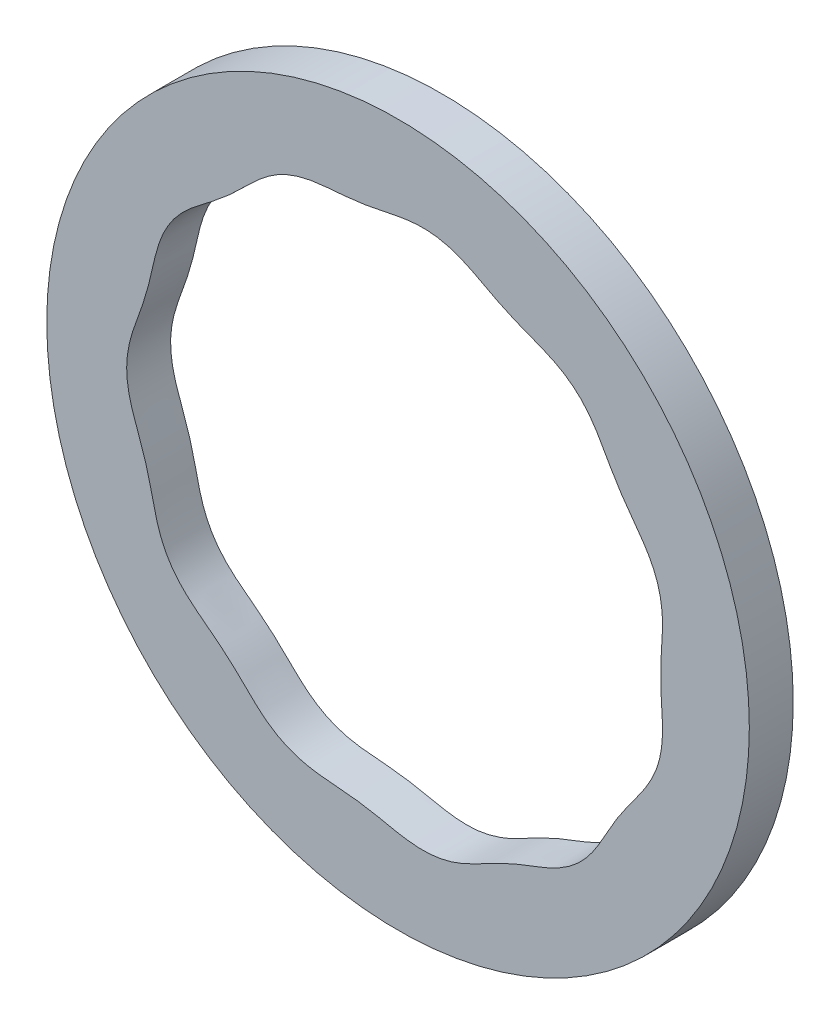
SolidWorks part; units mm, degrees
ref_plane "Front Plane" through (0, 0, 0) normal (0, 0, 1) x (1, 0, 0)
ref_plane "Top Plane" through (0, 0, 0) normal (0, 1, 0) x (1, 0, 0)
ref_plane "Right Plane" through (0, 0, 0) normal (1, 0, 0) x (0, 0, -1)
curve "Curve1"
sketch "Sketch2" plane through (0, 0, 0) normal (0, 0, 1) x (1, 0, 0)
  circle A0 centre (0, 0) radius 40
  dimension "D1" = 80
extrude "Boss-Extrude1" add sketch "Sketch2" along normal blind 5
sketch "Sketch3" plane through (0, 0, 0) normal (0, 0, 1) x (1, 0, 0)
  spline S3 degree 3 poles (-28.7034, -8.3743) (-28.552, -8.8888) (-28.4221, -9.3767) (-28.1806, -10.3578) (-28.0695, -10.8512) (-27.7343, -12.3306) (-27.5067, -13.3158) (-27.0032, -14.7464) (-26.8088, -15.216) (-26.3514, -16.1336) (-26.0943, -16.5702) (-25.524, -17.3996) (-25.2108, -17.7924) (-24.5338, -18.5385) (-24.1697, -18.892) (-23.0226, -19.9074) (-22.197, -20.5141) (-20.9796, -21.4483) (-20.5771, -21.7635) (-19.7884, -22.4128) (-19.4023, -22.747) (-18.6463, -23.434) (-18.2767, -23.7872) (-17.5443, -24.5015) (-17.1816, -24.8627) (-16.4457, -25.573) (-16.0714, -25.9221) (-15.297, -26.5828) (-14.897, -26.8938) (-14.0618, -27.4626) (-13.6265, -27.7204) (-12.7155, -28.1751) (-12.2383, -28.3717) (-11.275, -28.6928) (-10.7852, -28.8195) (-9.7925, -29.0185) (-9.2896, -29.0909) (-8.2764, -29.2047) (-7.767, -29.2462) (-6.7486, -29.3279) (-6.2393, -29.3681) (-5.2235, -29.4685) (-4.7171, -29.5286) (-3.7078, -29.6751) (-3.2051, -29.7616) (-1.7009, -30.0495) (-0.7041, -30.2836) (0.8041, -30.543) (1.3092, -30.6129) (2.3275, -30.6954) (2.836, -30.7075) (3.8443, -30.662) (4.3451, -30.6049) (5.3398, -30.419) (5.837, -30.2889) (7.2863, -29.8095) (8.1988, -29.3688) (9.5468, -28.6609) (9.9933, -28.4184) (10.8906, -27.9434) (11.3418, -27.7116) (12.2541, -27.2703) (12.7153, -27.061) (13.6475, -26.6648) (14.1185, -26.4777) (15.5375, -25.9299) (16.4913, -25.5825) (17.8669, -24.9368) (18.3148, -24.7008) (19.171, -24.1782) (19.5807, -23.8911) (20.1642, -23.4174) (20.3537, -23.2524) (20.7222, -22.9078) (20.902, -22.7275) (21.4195, -22.1713) (21.7355, -21.7813) (22.6155, -20.5658) (23.1096, -19.6939) (23.8417, -18.3801) (24.0851, -17.9417) (24.5868, -17.0749) (24.8455, -16.6467) (25.3841, -15.8044) (25.664, -15.3903) (26.2401, -14.573) (26.5364, -14.1698) (27.4259, -12.9607) (28.018, -12.1541) (28.7724, -10.855) (28.9992, -10.4121) (29.3907, -9.5052) (29.5559, -9.0408) (29.8214, -8.0888) (29.9219, -7.5992) (30.0589, -6.6064) (30.0949, -6.1088) (30.131, -4.6134) (30.0588, -3.613) (29.9654, -2.1144) (29.9371, -1.6148) (29.9025, -0.6148) (29.8962, -0.1144) (29.9087, 0.8872) (29.9276, 1.3884) (29.9809, 2.3914) (30.0151, 2.8931) (30.1058, 4.3979) (30.1462, 5.4004) (30.0268, 6.8982) (29.9578, 7.3964) (29.7479, 8.3905) (29.6044, 8.8913) (29.0809, 10.3245) (28.6037, 11.2028) (27.5089, 12.8747) (26.8965, 13.6714) (26.0148, 14.8888) (25.7267, 15.2981) (25.1717, 16.1294) (24.9048, 16.5515) (24.3906, 17.4074) (24.1432, 17.8413) (23.6551, 18.7134) (23.4143, 19.1515) (22.6685, 20.4509) (22.1364, 21.2948) (21.332, 22.2599) (21.1636, 22.4494) (20.8165, 22.8142) (20.6377, 22.9896) (20.0862, 23.4945) (19.6978, 23.8027) (18.8821, 24.3659) (18.4546, 24.6207) (17.5673, 25.0859) (17.1075, 25.2959) (16.1782, 25.6862) (15.7073, 25.8675) (14.7645, 26.2284) (14.2929, 26.4082) (13.3575, 26.7851) (12.8938, 26.9824) (11.9771, 27.4004) (11.5242, 27.6211) (10.6265, 28.0807) (10.1816, 28.319) (9.2915, 28.7954) (8.8461, 29.0327) (7.9432, 29.4808) (7.4861, 29.6905) (6.5565, 30.0579) (6.0835, 30.216) (5.1174, 30.4684) (4.6224, 30.5628) (3.618, 30.6806) (3.1174, 30.7032) (2.1191, 30.6854) (1.6213, 30.6448) (0.6279, 30.5174) (0.1319, 30.4306) (-0.8571, 30.2373) (-1.3503, 30.1316) (-2.3377, 29.9276) (-2.832, 29.8298) (-3.824, 29.6568) (-4.3216, 29.582) (-5.3206, 29.4573) (-5.8218, 29.407) (-7.3284, 29.2767) (-8.3368, 29.217) (-9.8324, 29.0102) (-10.3301, 28.9206) (-11.3048, 28.6831) (-11.7811, 28.536) (-12.7089, 28.1773) (-13.1604, 27.9659) (-13.8187, 27.5999) (-14.0356, 27.4693) (-14.4577, 27.1962) (-14.6635, 27.0534) (-15.669, 26.3117) (-16.3964, 25.6276) (-17.4685, 24.5792) (-17.8233, 24.2266) (-18.5428, 23.5332) (-18.9074, 23.1922) (-19.6526, 22.5291) (-20.0334, 22.2072) (-20.8091, 21.5801) (-21.204, 21.2749) (-22.3947, 20.3661) (-23.1955, 19.7685) (-24.3044, 18.7634) (-24.6596, 18.4087) (-25.3153, 17.6645) (-25.6173, 17.2739) (-26.1656, 16.453) (-26.4117, 16.0226) (-26.849, 15.1225) (-27.036, 14.6609) (-27.5211, 13.2572) (-27.7432, 12.292) (-28.0714, 10.8427) (-28.1805, 10.3595) (-28.4165, 9.3983) (-28.5435, 8.9203) (-28.8213, 7.9713) (-28.9723, 7.5003) (-29.2924, 6.5636) (-29.4615, 6.0979) (-29.9694, 4.7009) (-30.3061, 3.7691) (-30.6611, 2.3275) (-30.755, 1.8399) (-30.8472, 1.0943) (-30.8696, 0.8448) (-30.8971, 0.3519) (-30.9022, 0.1074) (-30.8869, -1.1059) (-30.7403, -2.0467) (-30.265, -3.8876) (-29.9377, -4.788) (-29.4467, -6.1387) (-29.2835, -6.589) (-29.0519, -7.2675) (-28.9767, -7.4941) (-28.868, -7.8349) (-28.8323, -7.9486) (-28.7799, -8.1194) (-28.7626, -8.1764) (-28.7368, -8.2619) (-28.7283, -8.2905) (-28.7113, -8.3475) (-28.7034, -8.3743) (-28.552, -8.8888) (-28.4221, -9.3767) knots -0.000488 -0.000488 0 0 0.007812 0.007812 0.015625 0.015625 0.03125 0.03125 0.039062 0.039062 0.046875 0.046875 0.054687 0.054687 0.0625 0.0625 0.078125 0.078125 0.085937 0.085937 0.09375 0.09375 0.101562 0.101562 0.109375 0.109375 0.117187 0.117187 0.125 0.125 0.132812 0.132812 0.140625 0.140625 0.148437 0.148437 0.15625 0.15625 0.164062 0.164062 0.171875 0.171875 0.179687 0.179687 0.1875 0.1875 0.203125 0.203125 0.210937 0.210937 0.21875 0.21875 0.226562 0.226562 0.234375 0.234375 0.25 0.25 0.257812 0.257812 0.265625 0.265625 0.273437 0.273437 0.28125 0.28125 0.296875 0.296875 0.304687 0.304687 0.3125 0.3125 0.316406 0.316406 0.320312 0.320312 0.328125 0.328125 0.34375 0.34375 0.351562 0.351562 0.359375 0.359375 0.367187 0.367187 0.375 0.375 0.390625 0.390625 0.398437 0.398437 0.40625 0.40625 0.414062 0.414062 0.421875 0.421875 0.4375 0.4375 0.445312 0.445312 0.453125 0.453125 0.460937 0.460937 0.46875 0.46875 0.484375 0.484375 0.492187 0.492187 0.5 0.5 0.515625 0.515625 0.53125 0.53125 0.539062 0.539062 0.546875 0.546875 0.554687 0.554687 0.5625 0.5625 0.578125 0.578125 0.582031 0.582031 0.585937 0.585937 0.59375 0.59375 0.601562 0.601562 0.609375 0.609375 0.617187 0.617187 0.625 0.625 0.632812 0.632812 0.640625 0.640625 0.648437 0.648437 0.65625 0.65625 0.664062 0.664062 0.671875 0.671875 0.679687 0.679687 0.6875 0.6875 0.695312 0.695312 0.703125 0.703125 0.710937 0.710937 0.71875 0.71875 0.726562 0.726562 0.734375 0.734375 0.75 0.75 0.757812 0.757812 0.765625 0.765625 0.773437 0.773437 0.777344 0.777344 0.78125 0.78125 0.796875 0.796875 0.804687 0.804687 0.8125 0.8125 0.820312 0.820312 0.828125 0.828125 0.84375 0.84375 0.851562 0.851562 0.859375 0.859375 0.867187 0.867187 0.875 0.875 0.890625 0.890625 0.898437 0.898437 0.90625 0.90625 0.914062 0.914062 0.921875 0.921875 0.9375 0.9375 0.945312 0.945312 0.949219 0.949219 0.953125 0.953125 0.96875 0.96875 0.984375 0.984375 0.992187 0.992187 0.996094 0.996094 0.998047 0.998047 0.999023 0.999023 0.999512 0.999512 1 1 1.007812 1.007812 1.015625 only from (-28.6945, -8.4046) to (-28.6945, -8.4046)
  spline S4 degree 3 poles (-28.7034, -8.3743) (-28.552, -8.8888) (-28.4221, -9.3767) (-28.1806, -10.3578) (-28.0695, -10.8512) (-27.7343, -12.3306) (-27.5067, -13.3158) (-27.0032, -14.7464) (-26.8088, -15.216) (-26.3514, -16.1336) (-26.0943, -16.5702) (-25.524, -17.3996) (-25.2108, -17.7924) (-24.5338, -18.5385) (-24.1697, -18.892) (-23.0226, -19.9074) (-22.197, -20.5141) (-20.9796, -21.4483) (-20.5771, -21.7635) (-19.7884, -22.4128) (-19.4023, -22.747) (-18.6463, -23.434) (-18.2767, -23.7872) (-17.5443, -24.5015) (-17.1816, -24.8627) (-16.4457, -25.573) (-16.0714, -25.9221) (-15.297, -26.5828) (-14.897, -26.8938) (-14.0618, -27.4626) (-13.6265, -27.7204) (-12.7155, -28.1751) (-12.2383, -28.3717) (-11.275, -28.6928) (-10.7852, -28.8195) (-9.7925, -29.0185) (-9.2896, -29.0909) (-8.2764, -29.2047) (-7.767, -29.2462) (-6.7486, -29.3279) (-6.2393, -29.3681) (-5.2235, -29.4685) (-4.7171, -29.5286) (-3.7078, -29.6751) (-3.2051, -29.7616) (-1.7009, -30.0495) (-0.7041, -30.2836) (0.8041, -30.543) (1.3092, -30.6129) (2.3275, -30.6954) (2.836, -30.7075) (3.8443, -30.662) (4.3451, -30.6049) (5.3398, -30.419) (5.837, -30.2889) (7.2863, -29.8095) (8.1988, -29.3688) (9.5468, -28.6609) (9.9933, -28.4184) (10.8906, -27.9434) (11.3418, -27.7116) (12.2541, -27.2703) (12.7153, -27.061) (13.6475, -26.6648) (14.1185, -26.4777) (15.5375, -25.9299) (16.4913, -25.5825) (17.8669, -24.9368) (18.3148, -24.7008) (19.171, -24.1782) (19.5807, -23.8911) (20.1642, -23.4174) (20.3537, -23.2524) (20.7222, -22.9078) (20.902, -22.7275) (21.4195, -22.1713) (21.7355, -21.7813) (22.6155, -20.5658) (23.1096, -19.6939) (23.8417, -18.3801) (24.0851, -17.9417) (24.5868, -17.0749) (24.8455, -16.6467) (25.3841, -15.8044) (25.664, -15.3903) (26.2401, -14.573) (26.5364, -14.1698) (27.4259, -12.9607) (28.018, -12.1541) (28.7724, -10.855) (28.9992, -10.4121) (29.3907, -9.5052) (29.5559, -9.0408) (29.8214, -8.0888) (29.9219, -7.5992) (30.0589, -6.6064) (30.0949, -6.1088) (30.131, -4.6134) (30.0588, -3.613) (29.9654, -2.1144) (29.9371, -1.6148) (29.9025, -0.6148) (29.8962, -0.1144) (29.9087, 0.8872) (29.9276, 1.3884) (29.9809, 2.3914) (30.0151, 2.8931) (30.1058, 4.3979) (30.1462, 5.4004) (30.0268, 6.8982) (29.9578, 7.3964) (29.7479, 8.3905) (29.6044, 8.8913) (29.0809, 10.3245) (28.6037, 11.2028) (27.5089, 12.8747) (26.8965, 13.6714) (26.0148, 14.8888) (25.7267, 15.2981) (25.1717, 16.1294) (24.9048, 16.5515) (24.3906, 17.4074) (24.1432, 17.8413) (23.6551, 18.7134) (23.4143, 19.1515) (22.6685, 20.4509) (22.1364, 21.2948) (21.332, 22.2599) (21.1636, 22.4494) (20.8165, 22.8142) (20.6377, 22.9896) (20.0862, 23.4945) (19.6978, 23.8027) (18.8821, 24.3659) (18.4546, 24.6207) (17.5673, 25.0859) (17.1075, 25.2959) (16.1782, 25.6862) (15.7073, 25.8675) (14.7645, 26.2284) (14.2929, 26.4082) (13.3575, 26.7851) (12.8938, 26.9824) (11.9771, 27.4004) (11.5242, 27.6211) (10.6265, 28.0807) (10.1816, 28.319) (9.2915, 28.7954) (8.8461, 29.0327) (7.9432, 29.4808) (7.4861, 29.6905) (6.5565, 30.0579) (6.0835, 30.216) (5.1174, 30.4684) (4.6224, 30.5628) (3.618, 30.6806) (3.1174, 30.7032) (2.1191, 30.6854) (1.6213, 30.6448) (0.6279, 30.5174) (0.1319, 30.4306) (-0.8571, 30.2373) (-1.3503, 30.1316) (-2.3377, 29.9276) (-2.832, 29.8298) (-3.824, 29.6568) (-4.3216, 29.582) (-5.3206, 29.4573) (-5.8218, 29.407) (-7.3284, 29.2767) (-8.3368, 29.217) (-9.8324, 29.0102) (-10.3301, 28.9206) (-11.3048, 28.6831) (-11.7811, 28.536) (-12.7089, 28.1773) (-13.1604, 27.9659) (-13.8187, 27.5999) (-14.0356, 27.4693) (-14.4577, 27.1962) (-14.6635, 27.0534) (-15.669, 26.3117) (-16.3964, 25.6276) (-17.4685, 24.5792) (-17.8233, 24.2266) (-18.5428, 23.5332) (-18.9074, 23.1922) (-19.6526, 22.5291) (-20.0334, 22.2072) (-20.8091, 21.5801) (-21.204, 21.2749) (-22.3947, 20.3661) (-23.1955, 19.7685) (-24.3044, 18.7634) (-24.6596, 18.4087) (-25.3153, 17.6645) (-25.6173, 17.2739) (-26.1656, 16.453) (-26.4117, 16.0226) (-26.849, 15.1225) (-27.036, 14.6609) (-27.5211, 13.2572) (-27.7432, 12.292) (-28.0714, 10.8427) (-28.1805, 10.3595) (-28.4165, 9.3983) (-28.5435, 8.9203) (-28.8213, 7.9713) (-28.9723, 7.5003) (-29.2924, 6.5636) (-29.4615, 6.0979) (-29.9694, 4.7009) (-30.3061, 3.7691) (-30.6611, 2.3275) (-30.755, 1.8399) (-30.8472, 1.0943) (-30.8696, 0.8448) (-30.8971, 0.3519) (-30.9022, 0.1074) (-30.8869, -1.1059) (-30.7403, -2.0467) (-30.265, -3.8876) (-29.9377, -4.788) (-29.4467, -6.1387) (-29.2835, -6.589) (-29.0519, -7.2675) (-28.9767, -7.4941) (-28.868, -7.8349) (-28.8323, -7.9486) (-28.7799, -8.1194) (-28.7626, -8.1764) (-28.7368, -8.2619) (-28.7283, -8.2905) (-28.7113, -8.3475) (-28.7034, -8.3743) (-28.552, -8.8888) (-28.4221, -9.3767) knots -0.000488 -0.000488 0 0 0.007812 0.007812 0.015625 0.015625 0.03125 0.03125 0.039062 0.039062 0.046875 0.046875 0.054687 0.054687 0.0625 0.0625 0.078125 0.078125 0.085937 0.085937 0.09375 0.09375 0.101562 0.101562 0.109375 0.109375 0.117187 0.117187 0.125 0.125 0.132812 0.132812 0.140625 0.140625 0.148437 0.148437 0.15625 0.15625 0.164062 0.164062 0.171875 0.171875 0.179687 0.179687 0.1875 0.1875 0.203125 0.203125 0.210937 0.210937 0.21875 0.21875 0.226562 0.226562 0.234375 0.234375 0.25 0.25 0.257812 0.257812 0.265625 0.265625 0.273437 0.273437 0.28125 0.28125 0.296875 0.296875 0.304687 0.304687 0.3125 0.3125 0.316406 0.316406 0.320312 0.320312 0.328125 0.328125 0.34375 0.34375 0.351562 0.351562 0.359375 0.359375 0.367187 0.367187 0.375 0.375 0.390625 0.390625 0.398437 0.398437 0.40625 0.40625 0.414062 0.414062 0.421875 0.421875 0.4375 0.4375 0.445312 0.445312 0.453125 0.453125 0.460937 0.460937 0.46875 0.46875 0.484375 0.484375 0.492187 0.492187 0.5 0.5 0.515625 0.515625 0.53125 0.53125 0.539062 0.539062 0.546875 0.546875 0.554687 0.554687 0.5625 0.5625 0.578125 0.578125 0.582031 0.582031 0.585937 0.585937 0.59375 0.59375 0.601562 0.601562 0.609375 0.609375 0.617187 0.617187 0.625 0.625 0.632812 0.632812 0.640625 0.640625 0.648437 0.648437 0.65625 0.65625 0.664062 0.664062 0.671875 0.671875 0.679687 0.679687 0.6875 0.6875 0.695312 0.695312 0.703125 0.703125 0.710937 0.710937 0.71875 0.71875 0.726562 0.726562 0.734375 0.734375 0.75 0.75 0.757812 0.757812 0.765625 0.765625 0.773437 0.773437 0.777344 0.777344 0.78125 0.78125 0.796875 0.796875 0.804687 0.804687 0.8125 0.8125 0.820312 0.820312 0.828125 0.828125 0.84375 0.84375 0.851562 0.851562 0.859375 0.859375 0.867187 0.867187 0.875 0.875 0.890625 0.890625 0.898437 0.898437 0.90625 0.90625 0.914062 0.914062 0.921875 0.921875 0.9375 0.9375 0.945312 0.945312 0.949219 0.949219 0.953125 0.953125 0.96875 0.96875 0.984375 0.984375 0.992187 0.992187 0.996094 0.996094 0.998047 0.998047 0.999023 0.999023 0.999512 0.999512 1 1 1.007812 1.007812 1.015625 only from (-28.6945, -8.4046) to (-28.6945, -8.4046)
  dimension "D1" = 0.4
extrude "Cut-Extrude1" cut sketch "Sketch3" along normal through all
